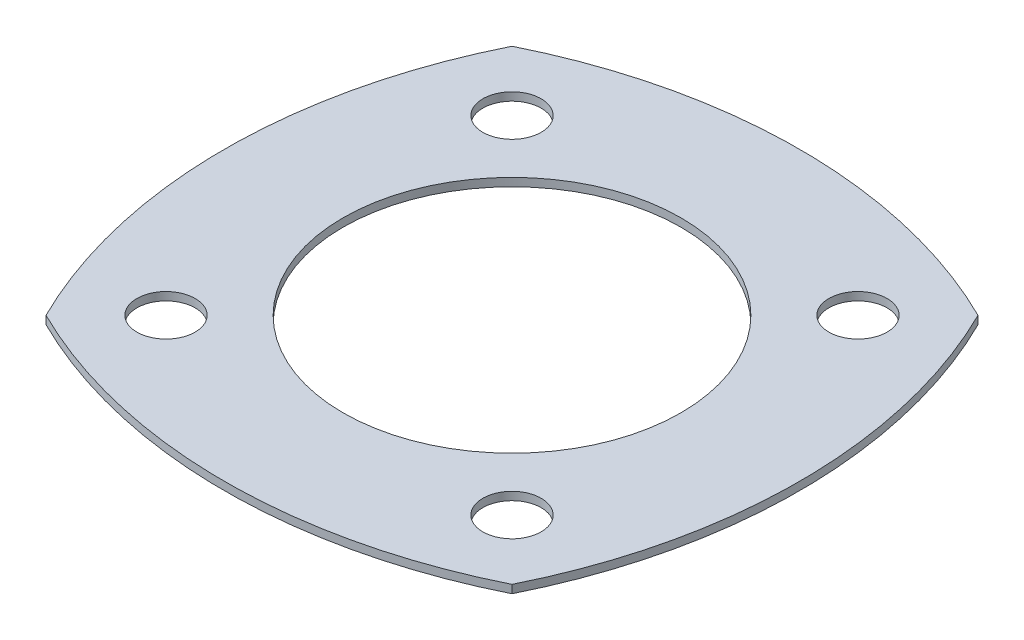
SolidWorks part; units mm, degrees
ref_plane "Front Plane" through (0, 0, 0) normal (0, 0, 1) x (1, 0, 0)
ref_plane "Top Plane" through (0, 0, 0) normal (0, 1, 0) x (1, 0, 0)
ref_plane "Right Plane" through (0, 0, 0) normal (1, 0, 0) x (0, 0, -1)
sketch "Sketch1" plane through (0, 0, 0) normal (0, 1, 0) x (1, 0, 0)
  arc A0 (10, -10) -> (10, 10) centre (-10.1556, 0) ccw
  arc A1 (10, 10) -> (-10, 10) centre (0, -10.1556) ccw
  arc A2 (-10, 10) -> (-10, -10) centre (10.1556, 0) ccw
  arc A3 (-10, -10) -> (10, -10) centre (0, 10.1556) ccw
  circle A4 centre (0, 0) radius 7.25
  circle A5 centre (7.4246, 7.4246) radius 1.25
  circle A6 centre (7.4246, -7.4246) radius 1.25
  circle A7 centre (-7.4246, -7.4246) radius 1.25
  circle A8 centre (-7.4246, 7.4246) radius 1.25
extrude "Boss-Extrude1" add sketch "Sketch1" along normal blind 0.35
